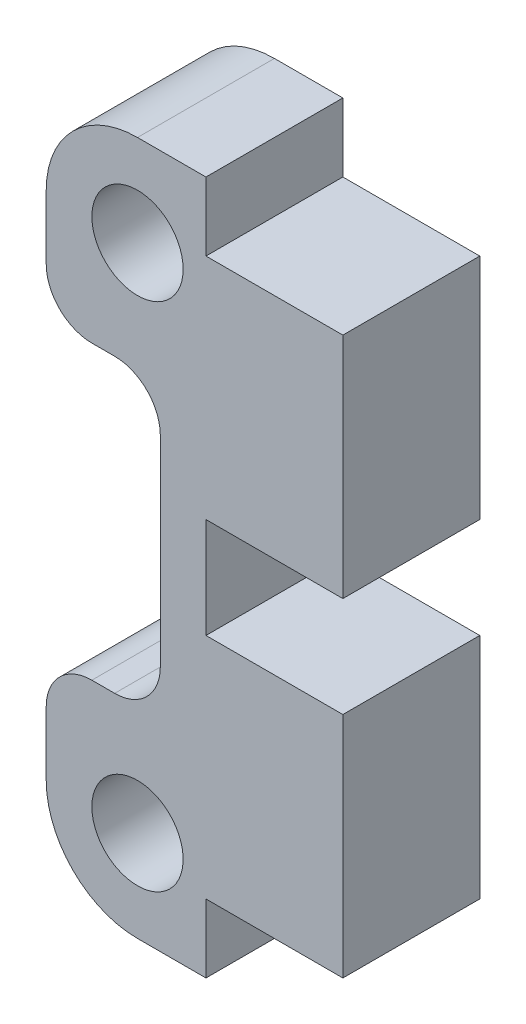
SolidWorks part; units mm, degrees
ref_plane "Plan de face" through (0, 0, 0) normal (0, 0, 1) x (1, 0, 0)
ref_plane "Plan de dessus" through (0, 0, 0) normal (0, 1, 0) x (1, 0, 0)
ref_plane "Plan de droite" through (0, 0, 0) normal (1, 0, 0) x (0, 0, -1)
sketch "Esquisse1" plane through (0, 0, 0) normal (0, 0, 1) x (1, 0, 0)
  line L0 (0, 20.7023) -> (0, -19.8769) construction
  line L1 (-32.3664, 0) -> (30.3594, 0) construction
  line L2 (-8.9997, 15.2) -> (-5.9997, 15.2)
  line L3 (-12.9997, 11.2) -> (-12.9997, 8.3964)
  line L4 (-10.9997, 6.3964) -> (-10, 6.3964)
  line L5 (0, 2.2) -> (-5.9997, 2.2)
  line L6 (-5.9997, 2.2) -> (-5.9997, -2.2)
  line L7 (-8, 4.3964) -> (-8, -4.3964)
  line L8 (0, 2.2) -> (0.0003, 2.2)
  line L9 (0.0003, 2.2) -> (0.0003, 12.2)
  line L10 (-5.9997, -12.2) -> (-5.9997, -15.2)
  line L11 (0.0003, 12.2) -> (-5.9997, 12.2)
  line L12 (0.0003, -12.2) -> (-5.9997, -12.2)
  line L13 (0.0003, -2.2) -> (0.0003, -12.2)
  line L14 (0, -2.2) -> (0.0003, -2.2)
  line L15 (0, -2.2) -> (-5.9997, -2.2)
  line L16 (-10.9997, -6.3964) -> (-10, -6.3964)
  line L17 (-12.9997, -11.2) -> (-12.9997, -8.3964)
  line L18 (-5.9997, 12.2) -> (-5.9997, 15.2)
  line L19 (-8.9997, -15.2) -> (-5.9997, -15.2)
  circle A0 centre (-8.9997, 11.2) radius 2
  arc A1 (-12.9997, 11.2) -> (-8.9997, 15.2) centre (-8.9997, 11.2) cw
  arc A2 (-12.9997, 8.3964) -> (-10.9997, 6.3964) centre (-10.9997, 8.3964) ccw
  arc A3 (-10, 6.3964) -> (-8, 4.3964) centre (-10, 4.3964) cw
  arc A4 (-10, -6.3964) -> (-8, -4.3964) centre (-10, -4.3964) ccw
  arc A5 (-12.9997, -8.3964) -> (-10.9997, -6.3964) centre (-10.9997, -8.3964) cw
  arc A6 (-12.9997, -11.2) -> (-8.9997, -15.2) centre (-8.9997, -11.2) ccw
  circle A7 centre (-8.9997, -11.2) radius 2
  point P11 (-8, 0)
  point P15 (-7.9997, -6.3964)
  point P19 (-13, 15.2)
  point P22 (-12.9997, 6.3964)
  point P25 (-7.9997, 6.3964)
  point P42 (0, 0)
  point P43 (-8, 0)
  point P44 (-5.9997, 0)
  point P45 (-12.9997, -6.3964)
  point P48 (-13, -15.2)
  dimension "D4" = 4
  dimension "D12" = 4
  dimension "D13" = 2
  dimension "D14" = 2
  dimension "D2" = 6
  dimension "D3" = 13
  dimension "D5" = 4
  dimension "D6" = 5.9997
  dimension "D7" = 4
  dimension "D8" = 22.4
  dimension "D9" = 8.8036
  dimension "D10" = 10
  dimension "D11" = 5
extrude "Boss.-Extru.1" add sketch "Esquisse1" along normal blind 6
